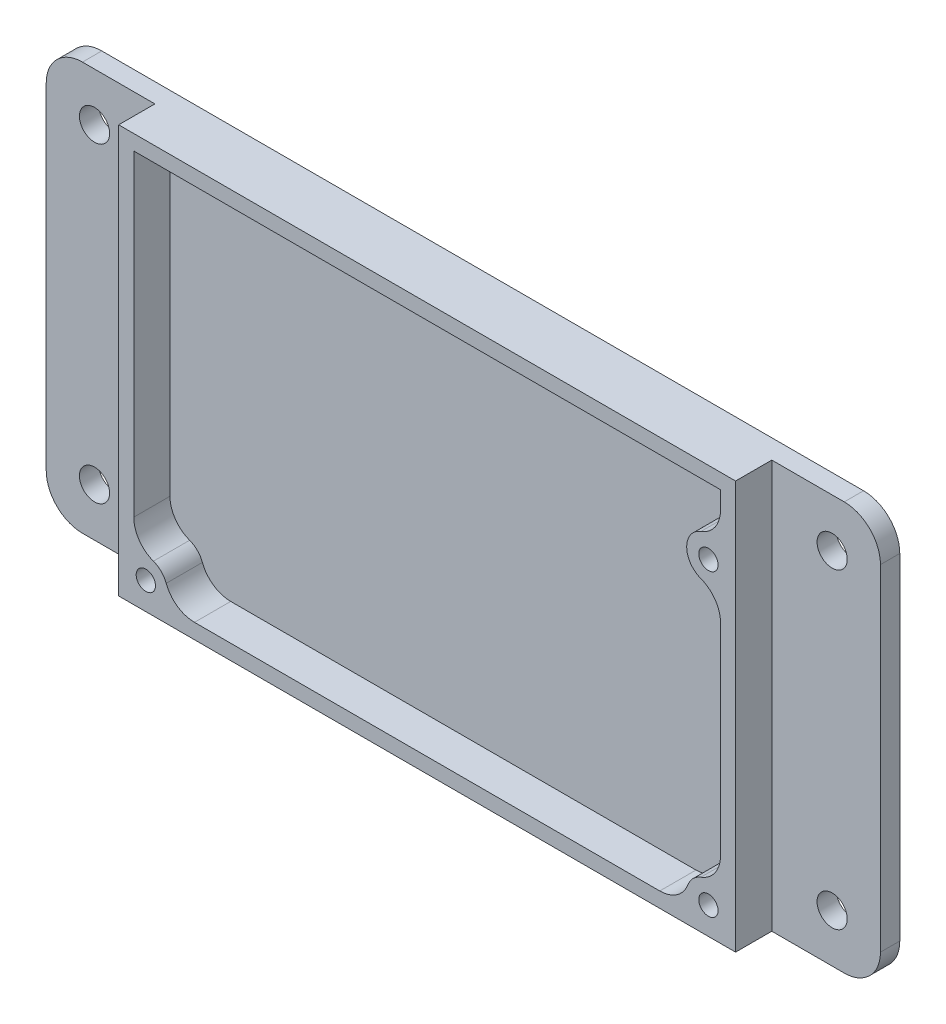
SolidWorks part; units mm, degrees
ref_plane "Front Plane" through (0, 0, 0) normal (0, 0, 1) x (1, 0, 0)
ref_plane "Top Plane" through (0, 0, 0) normal (0, 1, 0) x (1, 0, 0)
ref_plane "Right Plane" through (0, 0, 0) normal (1, 0, 0) x (0, 0, -1)
sketch "Sketch1" plane through (0, 0, 0) normal (0, 0, 1) x (1, 0, 0)
  line L1 (0, 0) -> (102.2, 0)
  line L2 (0, 0) -> (0, 67.6)
  line L3 (0, 67.6) -> (102.2, 67.6)
  line L4 (102.2, 0) -> (102.2, 67.6)
  line L5 (2.5, 2.5) -> (99.7, 2.5)
  line L6 (2.5, 2.5) -> (2.5, 65.1)
  line L7 (2.5, 65.1) -> (99.7, 65.1)
  line L8 (99.7, 2.5) -> (99.7, 65.1)
  circle A0 centre (4.5, 4.5) radius 1.6
  circle A1 centre (4.5, 4.5) radius 3.6
  circle A2 centre (97.7, 4.5) radius 1.6
  circle A3 centre (97.7, 4.5) radius 3.6
  circle A4 centre (97.7, 54.1) radius 1.6
  circle A5 centre (97.7, 54.1) radius 3.6
  dimension "D7" = 3.2
  dimension "D11" = 3.2
  dimension "D16" = 3.2
  dimension "D1" = 102.2
  dimension "D2" = 67.6
  dimension "D3" = 2.5
  dimension "D4" = 2.5
  dimension "D5" = 2.5
  dimension "D6" = 2.5
  dimension "D8" = 2
  dimension "D9" = 4.5
  dimension "D10" = 4.5
  dimension "D12" = 2
  dimension "D13" = 4.5
  dimension "D14" = 4.5
  dimension "D15" = 2
  dimension "D17" = 49.6
extrude "Boss-Extrude1" add sketch "Sketch1" along normal blind 6 contours L1 L4 L3 L2 A5 L8 A3 L5 A1 L6 L7 | L8 A5 A4 | L8 A3 L5 A2 | L5 A1 L6 A0 | L6 A1 L5 | L5 A3 L8 | L8 A5
sketch "Sketch2" plane through (0, 0, 0) normal (0, 0, -1) x (-1, 0, 0)
  line L0 (0, 67.6) -> (-102.2, 67.6) construction
  line L1 (-120.2, 0) -> (18, 0)
  line L2 (-120.2, 0) -> (-120.2, 67.6)
  line L3 (-120.2, 67.6) -> (18, 67.6)
  line L4 (18, 0) -> (18, 67.6)
  line L5 (0, 0) -> (-102.2, 0) construction
  line L7 (-51.1, 67.6) -> (-51.1, 0) construction
  circle A0 centre (-112.2, 59.6) radius 2.5
  circle A1 centre (-112.2, 8) radius 2.5
  circle A2 centre (10, 8) radius 2.5
  circle A3 centre (10, 59.6) radius 2.5
  dimension "D3" = 5
  dimension "D4" = 5
  dimension "D1" = 18
  dimension "D2" = 18
  dimension "D6" = 8
  dimension "D7" = 8
  dimension "D5" = 8
extrude "Boss-Extrude2" add sketch "Sketch2" along normal blind 3.2
fillet "Fillet1" radius 6 4 edges at (120.2, 67.6, -1.6) (120.2, 0, -1.6) (-18, 67.6, -1.6) (-18, 0, -1.6)
fillet "Fillet2" radius 5 2 edges at (99.7, 51.1067, 3) (99.7, 57.0933, 3)
fillet "Fillet3" radius 5 4 edges at (7.4933, 2.5, 3) (2.5, 7.4933, 3) (94.7067, 2.5, 3) (99.7, 7.4933, 3)
equation "\"M3HoleInner\"= 3.2mm"
equation "\"M3HoleThickness\"= 2mm"
equation "\"M3DistY\"= 49.6mm"
equation "\"M3DistX\"= 93mm"
equation "\"BoardX\"= 102.2mm"
equation "\"BoardY\"= 67.6mm"
equation "\"D1@Sketch1\"=\"BoardX\""
equation "\"D2@Sketch1\"=\"BoardY\""
equation "\"BoardThickness\"= 2.5mm"
equation "\"D3@Sketch1\"=\"BoardThickness\""
equation "\"D4@Sketch1\"=\"BoardThickness\""
equation "\"D5@Sketch1\"=\"BoardThickness\""
equation "\"D6@Sketch1\"=\"BoardThickness\""
equation "\"D7@Sketch1\"=\"M3HoleInner\""
equation "\"D8@Sketch1\"=\"M3HoleThickness\""
equation "\"D11@Sketch1\"=\"M3HoleInner\""
equation "\"D12@Sketch1\"=\"M3HoleThickness\""
equation "\"D15@Sketch1\"=\"M3HoleThickness\""
equation "\"D16@Sketch1\"=\"M3HoleInner\""
equation "\"D17@Sketch1\"=\"M3DistY\""
equation "\"MountFlangWidth\"= 18mm"
equation "\"MountFlangHoles\"= 5.0mm"
equation "\"D1@Sketch2\"=\"MountFlangWidth\""
equation "\"D2@Sketch2\"=\"MountFlangWidth\""
equation "\"D3@Sketch2\"=\"MountFlangHoles\""
equation "\"D4@Sketch2\"=\"MountFlangHoles\""
equation "\"D7@Sketch2\"=8"
